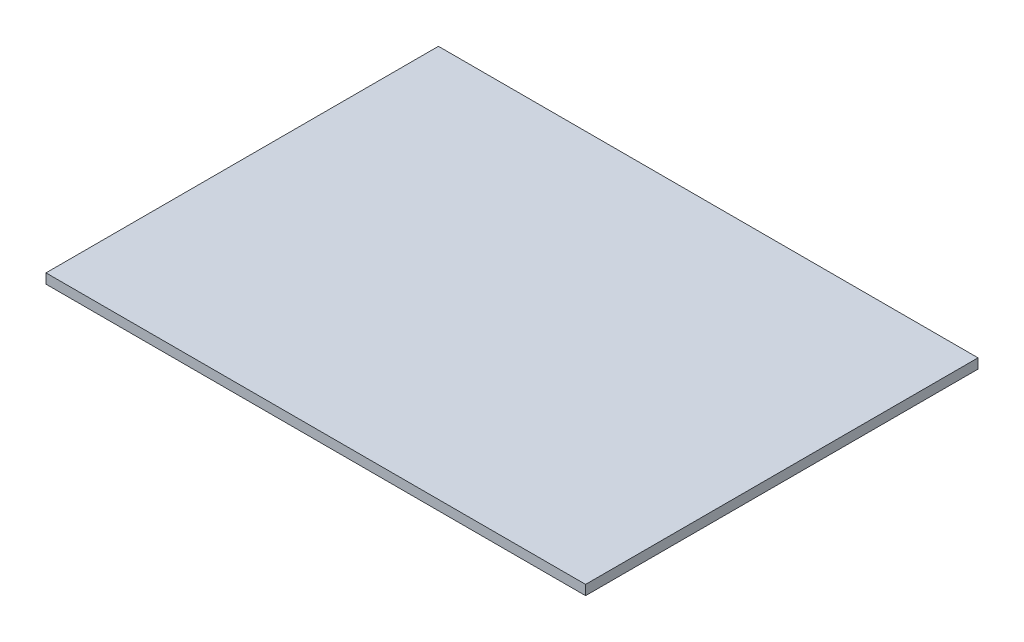
SolidWorks part; units mm, degrees
ref_plane "Front Plane" through (0, 0, 0) normal (0, 0, 1) x (1, 0, 0)
ref_plane "Top Plane" through (0, 0, 0) normal (0, 1, 0) x (1, 0, 0)
ref_plane "Right Plane" through (0, 0, 0) normal (1, 0, 0) x (0, 0, -1)
sketch "Sketch1" plane through (0, 0, 0) normal (0, 1, 0) x (1, 0, 0)
  line L1 (0, 0) -> (5500, 0)
  line L2 (0, 0) -> (0, 4000)
  line L3 (0, 4000) -> (5500, 4000)
  line L4 (5500, 0) -> (5500, 4000)
extrude "Boss-Extrude1" add sketch "Sketch1" along normal blind 100
